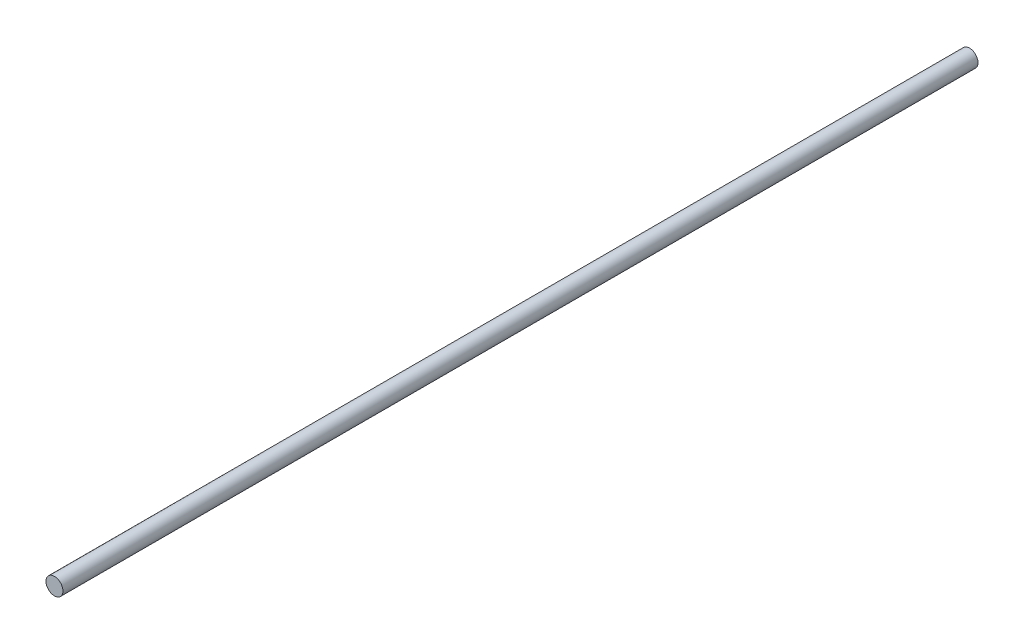
SolidWorks part; units mm, degrees
ref_plane "Front Plane" through (0, 0, 0) normal (0, 0, 1) x (1, 0, 0)
ref_plane "Top Plane" through (0, 0, 0) normal (0, 1, 0) x (1, 0, 0)
ref_plane "Right Plane" through (0, 0, 0) normal (1, 0, 0) x (0, 0, -1)
sketch "Sketch1" plane through (0, 0, 0) normal (0, 0, 1) x (1, 0, 0)
  circle A0 centre (0, 0) radius 3.9688
  dimension "D1" = 7.9375
extrude "Boss-Extrude1" add sketch "Sketch1" along normal blind 428.625
